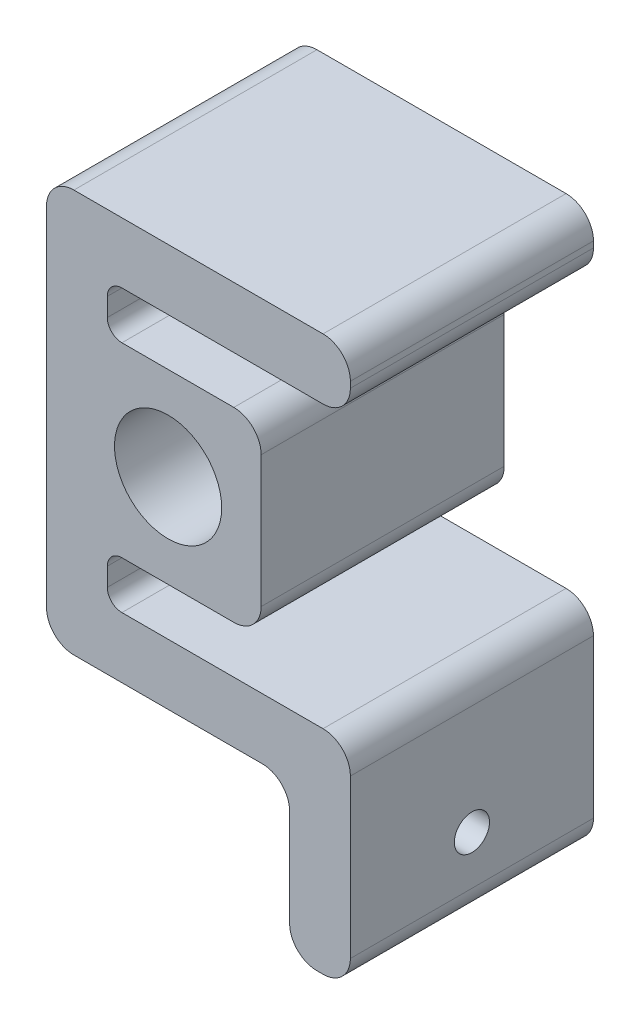
SolidWorks part; units mm, degrees
material "Bambu PAHT-CF"
ref_plane "Front Plane" through (0, 0, 0) normal (0, 0, 1) x (1, 0, 0)
ref_plane "Top Plane" through (0, 0, 0) normal (0, 1, 0) x (1, 0, 0)
ref_plane "Right Plane" through (0, 0, 0) normal (1, 0, 0) x (0, 0, -1)
sketch "Sketch1" plane through (0, 0, 0) normal (0, 0, 1) x (1, 0, 0)
  line L0 (-25.4, -36.365) -> (-25.4, 36.365)
  line L1 (-19.685, -42.08) -> (19.685, -42.08)
  line L2 (38.1, -68.115) -> (38.1, -35.095)
  line L3 (32.385, -29.38) -> (-9.652, -29.38)
  line L4 (-12.7, -26.332) -> (-12.7, -22.503)
  line L5 (-9.652, -19.455) -> (0, -19.455)
  line L6 (-9.652, 19.455) -> (0, 19.455)
  line L7 (-12.7, 22.503) -> (-12.7, 26.332)
  line L8 (-9.652, 29.38) -> (32.385, 29.38)
  line L9 (38.1, 35.095) -> (38.1, 36.365)
  line L10 (32.385, 42.08) -> (-19.685, 42.08)
  line L15 (0, -11.2) -> (0, -19.455) construction
  line L16 (0, 11.2) -> (0, 19.455) construction
  line L17 (11.2, 0) -> (19.455, 0) construction
  line L18 (0, 19.455) -> (13.74, 19.455)
  line L19 (19.455, 13.74) -> (19.455, 0)
  line L20 (19.455, 0) -> (19.455, -13.74)
  line L21 (13.74, -19.455) -> (0, -19.455)
  line L24 (32.385, -73.83) -> (31.115, -73.83)
  line L25 (25.4, -68.115) -> (25.4, -47.795)
  circle A0 centre (0, 0) radius 11.2
  arc A3 (-19.685, 42.08) -> (-25.4, 36.365) centre (-19.685, 36.365) ccw
  arc A4 (38.1, 36.365) -> (32.385, 42.08) centre (32.385, 36.365) ccw
  arc A6 (32.385, 29.38) -> (38.1, 35.095) centre (32.385, 35.095) ccw
  arc A7 (38.1, -35.095) -> (32.385, -29.38) centre (32.385, -35.095) ccw
  arc A8 (19.455, -13.74) -> (13.74, -19.455) centre (13.74, -13.74) cw
  arc A9 (13.74, 19.455) -> (19.455, 13.74) centre (13.74, 13.74) cw
  arc A10 (-12.7, 26.332) -> (-9.652, 29.38) centre (-9.652, 26.332) cw
  arc A11 (-9.652, 19.455) -> (-12.7, 22.503) centre (-9.652, 22.503) cw
  arc A12 (-12.7, -22.503) -> (-9.652, -19.455) centre (-9.652, -22.503) cw
  arc A13 (-9.652, -29.38) -> (-12.7, -26.332) centre (-9.652, -26.332) cw
  arc A16 (-25.4, -36.365) -> (-19.685, -42.08) centre (-19.685, -36.365) ccw
  arc A17 (19.685, -42.08) -> (25.4, -47.795) centre (19.685, -47.795) cw
  arc A18 (38.1, -68.115) -> (32.385, -73.83) centre (32.385, -68.115) cw
  arc A19 (31.115, -73.83) -> (25.4, -68.115) centre (31.115, -68.115) cw
  point P12 (0, 11.2)
  point P18 (-25.4, -42.08)
  point P19 (-25.4, -42.08)
  point P20 (0, -11.2)
  point P22 (11.2, 0)
  point P34 (38.1, -42.08)
  point P45 (-12.7, 29.38)
  point P48 (-12.7, 19.455)
  point P53 (-12.7, -29.38)
  point P57 (25.4, -42.08)
  point P60 (38.1, -73.83)
  point P63 (25.4, -73.83)
  dimension "D1" = 22.4
  dimension "D11" = 3.048
  dimension "D9" = 5.715
  dimension "D13" = 31.75
  dimension "D14" = 5.715
  dimension "D15" = 5.715
  dimension "D2" = 25.4
  dimension "D3" = 8.255
  dimension "D4" = 9.925
  dimension "D5" = 12.7
  dimension "D6" = 9.925
  dimension "D7" = 12.7
  dimension "D8" = 12.7
  dimension "D10" = 63.5
  dimension "D12" = 12.7
extrude "Boss-Extrude1" add sketch "Sketch1" along normal blind 50.8
sketch "Sketch2" plane through (25.4, 0, 0) normal (1, 0, 0) x (0, 0, -1)
  line L0 (-25.4, -68.115) -> (-25.4, -57.955) construction
  line L2 (-25.4, -57.955) -> (-25.4, -47.795) construction
  line L4 (-50.8, -47.795) -> (0, -47.795) construction
  line L5 (-50.8, -68.115) -> (0, -68.115) construction
  circle A0 centre (-25.4, -57.955) radius 3.675
  dimension "D1" = 7.35
extrude "Cut-Extrude1" cut sketch "Sketch2" along normal blind 50.8
